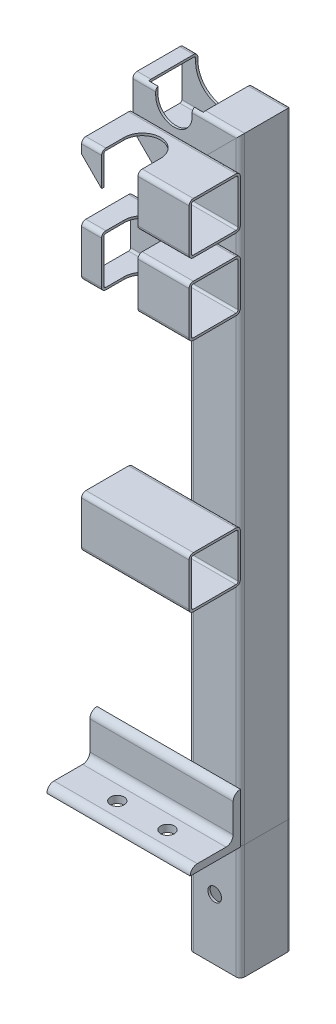
SolidWorks part; units mm, degrees
ref_plane "Front Plane" through (0, 0, 0) normal (0, 0, 1) x (1, 0, 0)
ref_plane "Top Plane" through (0, 0, 0) normal (0, 1, 0) x (1, 0, 0)
ref_plane "Right Plane" through (0, 0, 0) normal (1, 0, 0) x (0, 0, -1)
sketch "Sketch1" plane through (0, 0, 0) normal (0, 0, 1) x (1, 0, 0)
  line L0 (186.45, 0) -> (186.45, 412)
  line L1 (186.45, 412) -> (129.35, 412)
  line L2 (186.45, 0) -> (186.45, -80)
  dimension "D1" = 412
  dimension "D2" = 80
  dimension "D3" = 57.1
  dimension "D4" = 186.45
other "Structural Member1"
ref_plane "Plane1" through (186.45, 0, 0) normal (0, 1, 0) x (-1, 0, 0)
sketch "Sketch11" plane through (186.45, 0, 0) normal (0, 1, 0) x (-1, 0, 0)
  line L0 (-14.9, 16.3) -> (14.9, 16.3)
  line L1 (-14.9, 17.9) -> (14.9, 17.9)
  line L2 (-17.9, 14.9) -> (-17.9, -14.9)
  line L3 (-14.9, -17.9) -> (14.9, -17.9)
  line L4 (17.9, 14.9) -> (17.9, -14.9)
  line L5 (-17.9, 17.9) -> (17.9, -17.9) construction
  line L6 (-17.9, -17.9) -> (17.9, 17.9) construction
  line L7 (16.3, 14.9) -> (16.3, -14.9)
  line L8 (-14.9, -16.3) -> (14.9, -16.3)
  line L9 (-16.3, 14.9) -> (-16.3, -14.9)
  arc A0 (-17.9, -14.9) -> (-14.9, -17.9) centre (-14.9, -14.9) ccw
  arc A1 (14.9, -17.9) -> (17.9, -14.9) centre (14.9, -14.9) ccw
  arc A2 (17.9, 14.9) -> (14.9, 17.9) centre (14.9, 14.9) ccw
  arc A3 (-14.9, 17.9) -> (-17.9, 14.9) centre (-14.9, 14.9) ccw
  arc A4 (16.3, 14.9) -> (14.9, 16.3) centre (14.9, 14.9) ccw
  arc A5 (14.9, -16.3) -> (16.3, -14.9) centre (14.9, -14.9) ccw
  arc A6 (-16.3, -14.9) -> (-14.9, -16.3) centre (-14.9, -14.9) ccw
  arc A7 (-14.9, 16.3) -> (-16.3, 14.9) centre (-14.9, 14.9) ccw
  point P0 (0, 0)
  point P30 (0, 0)
  dimension "D3" = 3
  dimension "D1" = 35.8
  dimension "D2" = 35.8
  dimension "D4" = 1.6
sketch "Sketch12" plane through (0, 0, 0) normal (0, 0, 1) x (1, 0, 0)
  line L1 (158, 424.7) -> (158, 435.1) construction
  line L2 (145.3, 424.7) -> (145.3, 435.1)
  line L3 (170.7, 424.7) -> (170.7, 435.1)
  line L4 (186.45, 412) -> (129.35, 412) construction
  line L5 (129.35, 429.9) -> (204.35, 429.9) construction
  arc A0 (145.3, 424.7) -> (170.7, 424.7) centre (158, 424.7) ccw
  arc A1 (170.7, 435.1) -> (145.3, 435.1) centre (158, 435.1) ccw
  point P2 (158, 429.9)
  dimension "D1" = 25.4
  dimension "D2" = 158
extrude "Cut-Extrude1" cut sketch "Sketch12" against normal through all and the other way through all
sketch "Sketch13" plane through (0, 0, 0) normal (0, 1, 0) x (1, 0, 0)
  line L0 (104.35, -17.9) -> (204.35, -17.9)
  line L1 (170.7, -17.9) -> (201.35, -17.9) construction
  line L3 (204.35, 14.9) -> (204.35, -14.9) construction
  point P4 (154.35, -17.9)
  dimension "D1" = 100
other "Structural Member2"
ref_plane "Plane2" through (104.35, 0, 17.9) normal (1, 0, 0) x (0, 1, 0)
sketch "Sketch14" plane through (104.35, 0, 17.9) normal (1, 0, 0) x (0, 1, 0)
  line L0 (0, 0) -> (0, 35)
  line L1 (0, 17.5) -> (5, 17.5) construction
  line L2 (5, 30) -> (5, 10)
  line L3 (10, 5) -> (30, 5)
  line L4 (17.5, 5) -> (17.5, 0) construction
  line L5 (35, 0) -> (0, 0)
  arc A0 (35, 0) -> (30, 5) centre (30, 0) ccw
  arc A1 (0, 35) -> (5, 30) centre (0, 30) cw
  arc A2 (10, 5) -> (5, 10) centre (10, 10) cw
  point P10 (17.5, 0)
  point P14 (0, 17.5)
  point P15 (5, 17.5)
  point P16 (17.5, 5)
  point P17 (5, 35)
  point P18 (35, 5)
  point P21 (0, 0)
  dimension "D2" = 5
  dimension "D3" = 35
  dimension "Radius_1" = 5
  dimension "D1" = 5
sketch "Sketch15" plane through (0, 0, 0) normal (0, 1, 0) x (1, 0, 0)
  line L0 (154.35, -17.9) -> (154.35, -52.9) construction
  line L1 (204.35, -52.9) -> (104.35, -52.9) construction
  line L2 (-65.8005, -37.9) -> (374.5005, -37.9) construction
  line L3 (104.35, -17.9) -> (204.35, -17.9) construction
  line L4 (0, 28.933) -> (0, -28.933) construction
  circle A0 centre (138.5, -37.9) radius 4.7625
  circle A1 centre (173.5, -37.9) radius 4.7625
  point P7 (154.35, -37.9)
  point P16 (0, 0)
  dimension "D2" = 9.525
  dimension "D1" = 20
  dimension "D3" = 173.5
  dimension "D4" = 35
extrude "Cut-Extrude2" cut sketch "Sketch15" along normal through all
sketch "Sketch16" plane through (0, 0, 0) normal (0, 0, 1) x (1, 0, 0)
  line L4 (177.05, 424.7) -> (177.05, 435.1)
  line L5 (138.95, 435.1) -> (138.95, 424.7)
  line L6 (177.05, 424.7) -> (177.05, 435.1)
  line L7 (138.95, 435.1) -> (138.95, 424.7)
  arc A4 (138.95, 424.7) -> (177.05, 424.7) centre (158, 424.7) ccw
  arc A5 (177.05, 435.1) -> (138.95, 435.1) centre (158, 435.1) ccw
  arc A6 (138.95, 424.7) -> (177.05, 424.7) centre (158, 424.7) ccw
  arc A7 (177.05, 435.1) -> (138.95, 435.1) centre (158, 435.1) ccw
  dimension "D1" = 6.35
extrude "Cut-Extrude3" cut sketch "Sketch16" against normal through all and the other way up to surface
sketch "Sketch17" plane through (0, 0, 17.9) normal (0, 0, 1) x (1, 0, 0)
  line L0 (204.35, 408.4) -> (129.35, 408.4)
  line L1 (204.35, 429.9) -> (204.35, 0) construction
  line L2 (129.35, 397.1) -> (129.35, 426.9) construction
  line L4 (204.35, 358.4) -> (129.35, 358.4)
  line L5 (204.35, 194.4) -> (129.35, 194.4)
  dimension "D1" = 408.4
  dimension "D2" = 358.4
  dimension "D3" = 194.4
other "Structural Member3"
ref_plane "Plane3" through (204.35, 408.4, 17.9) normal (-1, 0, 0) x (0, -1, 0)
sketch "Sketch19" plane through (204.35, 390.5, 35.8) normal (-1, 0, 0) x (0, -1, 0)
  line L0 (-14.9, 16.3) -> (14.9, 16.3)
  line L1 (-14.9, 17.9) -> (14.9, 17.9)
  line L2 (-17.9, 14.9) -> (-17.9, -14.9)
  line L3 (-14.9, -17.9) -> (14.9, -17.9)
  line L4 (17.9, 14.9) -> (17.9, -14.9)
  line L5 (-17.9, 17.9) -> (17.9, -17.9) construction
  line L6 (-17.9, -17.9) -> (17.9, 17.9) construction
  line L7 (16.3, 14.9) -> (16.3, -14.9)
  line L8 (-14.9, -16.3) -> (14.9, -16.3)
  line L9 (-16.3, 14.9) -> (-16.3, -14.9)
  arc A0 (-17.9, -14.9) -> (-14.9, -17.9) centre (-14.9, -14.9) ccw
  arc A1 (14.9, -17.9) -> (17.9, -14.9) centre (14.9, -14.9) ccw
  arc A2 (17.9, 14.9) -> (14.9, 17.9) centre (14.9, 14.9) ccw
  arc A3 (-14.9, 17.9) -> (-17.9, 14.9) centre (-14.9, 14.9) ccw
  arc A4 (16.3, 14.9) -> (14.9, 16.3) centre (14.9, 14.9) ccw
  arc A5 (14.9, -16.3) -> (16.3, -14.9) centre (14.9, -14.9) ccw
  arc A6 (-16.3, -14.9) -> (-14.9, -16.3) centre (-14.9, -14.9) ccw
  arc A7 (-14.9, 16.3) -> (-16.3, 14.9) centre (-14.9, 14.9) ccw
  point P0 (0, 0)
  point P30 (0, 0)
  dimension "D3" = 3
  dimension "D1" = 35.8
  dimension "D2" = 35.8
  dimension "D4" = 1.6
sketch "Sketch20" plane through (0, 408.4, 0) normal (0, 1, 0) x (1, 0, 0)
  line L0 (156, -37.9) -> (156, -69.5) construction
  line L1 (168.7, -37.9) -> (168.7, -69.5)
  line L2 (143.3, -37.9) -> (143.3, -69.5)
  line L3 (129.35, -53.7) -> (204.35, -53.7) construction
  line L4 (104.35, -17.9) -> (204.35, -17.9) construction
  arc A0 (168.7, -37.9) -> (143.3, -37.9) centre (156, -37.9) ccw
  arc A1 (143.3, -69.5) -> (168.7, -69.5) centre (156, -69.5) ccw
  point P2 (156, -53.7)
  dimension "D1" = 156
  dimension "D2" = 25.4
  dimension "D3" = 20
extrude "Cut-Extrude4" cut sketch "Sketch20" against normal blind 300
sketch "Sketch21" plane through (0, 0, 0) normal (0, 0, 1) x (1, 0, 0)
  line L0 (129.35, 399.25) -> (156, 372.6)
  line L1 (143.3, 372.6) -> (168.7, 372.6) construction
  line L2 (129.35, 375.6) -> (129.35, 405.4) construction
  line L3 (156, 372.6) -> (156, 362.9763)
  line L4 (156, 362.9763) -> (122.4969, 362.9763)
  line L5 (122.4969, 362.9763) -> (122.4969, 399.25)
  line L6 (122.4969, 399.25) -> (129.35, 399.25)
  dimension "D1" = 45
extrude "Cut-Extrude5" cut sketch "Sketch21" along normal through all
sketch "Sketch22" plane through (0, 0, 17.9) normal (0, 0, 1) x (1, 0, 0)
  line L2 (104.35, 0) -> (204.35, 0) construction
  line L3 (186.45, 0) -> (186.45, -80) construction
  circle A0 centre (186.45, -37.5) radius 4.7625
  dimension "D1" = 9.525
  dimension "D2" = 37.5
  dimension "D3" = 186.45
extrude "Cut-Extrude6" cut sketch "Sketch22" against normal through all
